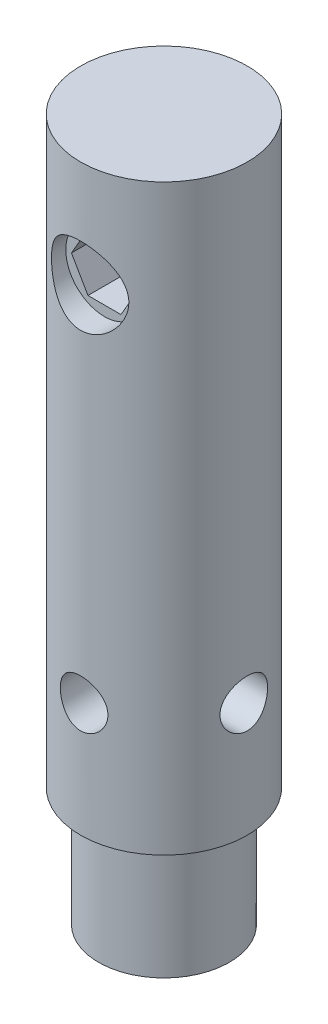
SolidWorks part; units mm, degrees
ref_plane "前视基准面" through (0, 0, 0) normal (0, 0, 1) x (1, 0, 0)
ref_plane "上视基准面" through (0, 0, 0) normal (0, 1, 0) x (1, 0, 0)
ref_plane "右视基准面" through (0, 0, 0) normal (1, 0, 0) x (0, 0, -1)
sketch "草图1" plane through (0, 0, 0) normal (0, 1, 0) x (1, 0, 0)
  circle A0 centre (0, 0) radius 14
  dimension "D1" = 28
extrude "凸台-拉伸1" add sketch "草图1" along normal blind 98
sketch "草图2" plane through (0, 0, 0) normal (0, 0, 1) x (1, 0, 0)
  line L1 (-14, 0) -> (14, 0) construction
  circle A0 centre (0, 80) radius 6.5
  circle A1 centre (0, 19.2) radius 4
  dimension "D1" = 13
  dimension "D2" = 80
  dimension "D3" = 8
  dimension "D4" = 19.2
extrude "切除-拉伸1" cut sketch "草图2" along normal mid plane 227
sketch "草图3" plane through (0, 0, 0) normal (0, 0, 1) x (1, 0, 0)
  line L0 (0, 129.4054) -> (0, 64.8867) construction
  line L13 (-35.9744, 80) -> (45.031, 80) construction
  line L14 (-14, 98) -> (-14, 0) construction
  line L15 (14, 0) -> (14, 98) construction
  line L17 (-14, 0) -> (14, 0) construction
  line L19 (5.55, 80) -> (2.775, 84.8064)
  line L20 (2.775, 84.8064) -> (-2.775, 84.8064)
  line L21 (-2.775, 84.8064) -> (-5.55, 80)
  line L22 (-5.55, 80) -> (-2.775, 75.1936)
  line L23 (-2.775, 75.1936) -> (2.775, 75.1936)
  line L24 (2.775, 75.1936) -> (5.55, 80)
  circle A1 centre (0, 80) radius 4.8064 construction
  circle A2 centre (0, 80) radius 5.55 construction
  circle A3 centre (0, 80) radius 7.5
  dimension "D1" = 80
  dimension "D2" = 11.1
  dimension "D3" = 15
extrude "凸台-拉伸2" add sketch "草图3" along normal mid plane 20
sketch "草图4" plane through (0, 0, 0) normal (0, -1, 0) x (1, 0, 0)
  circle A0 centre (0, 0) radius 11
  dimension "D1" = 22
extrude "凸台-拉伸4" add sketch "草图4" along normal blind 20
sketch "草图5" plane through (0, 0, 0) normal (1, 0, 0) x (0, 0, -1)
  line L0 (0, 157.3743) -> (0, -85.0773) construction
  line L1 (-11, 0) -> (11, 0) construction
  circle A0 centre (0, 19.2) radius 4
  dimension "D1" = 8
  dimension "D2" = 19.2
extrude "切除-拉伸2" cut sketch "草图5" against normal mid plane 40
